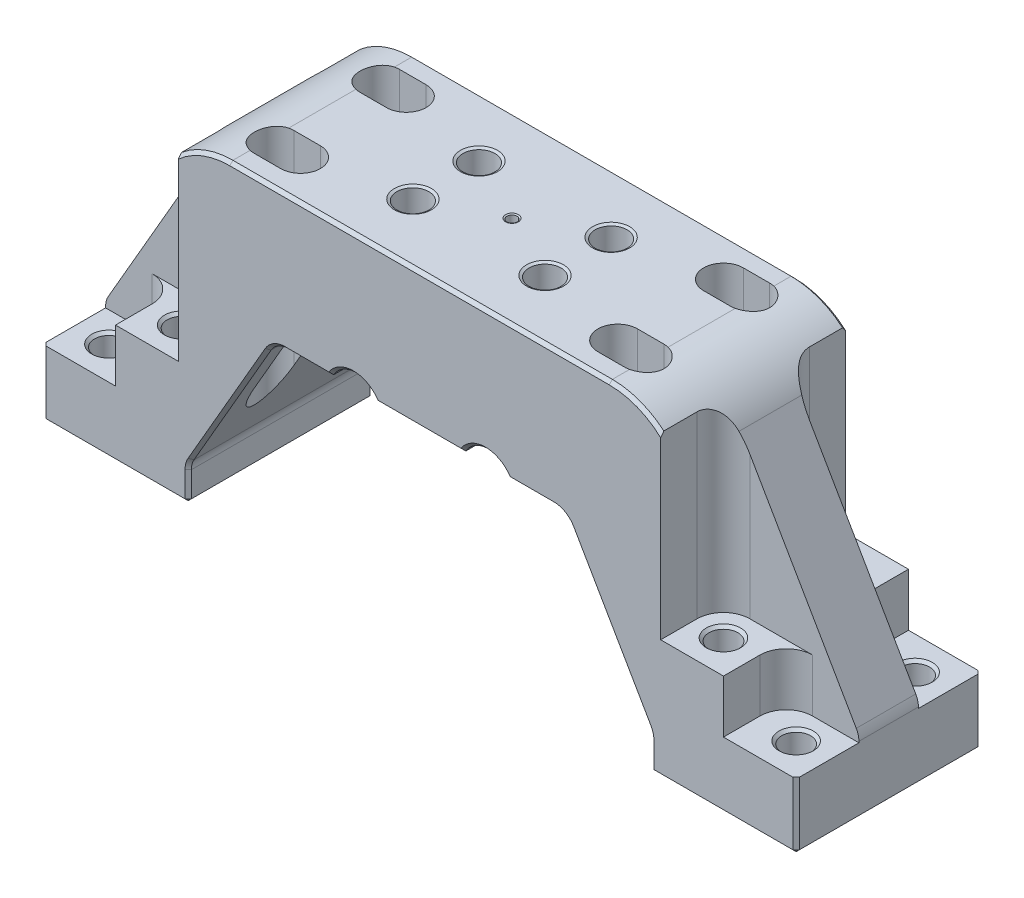
SolidWorks part; units mm, degrees
material "6061-T6 AL"
ref_plane "Front" through (0, 0, 0) normal (0, 0, 1) x (1, 0, 0)
ref_plane "Top" through (0, 0, 0) normal (0, 1, 0) x (1, 0, 0)
ref_plane "Right" through (0, 0, 0) normal (1, 0, 0) x (0, 0, -1)
sketch "Sketch1" plane through (0, 0, 0) normal (0, 0, 1) x (1, 0, 0)
  line L0 (-180.975, 0) -> (-111.125, 0)
  line L1 (-111.125, 0) -> (-111.125, 16.2087)
  line L2 (-111.125, 16.2087) -> (-70.0366, 87.376)
  line L3 (-70.0366, 87.376) -> (70.0366, 87.376)
  line L4 (70.0366, 87.376) -> (111.125, 16.2087)
  line L5 (111.125, 16.2087) -> (111.125, 0)
  line L6 (111.125, 0) -> (180.975, 0)
  line L7 (180.975, 0) -> (180.975, 34.925)
  line L8 (180.975, 34.925) -> (113.1508, 152.4)
  line L9 (113.1508, 152.4) -> (-113.1508, 152.4)
  line L10 (-113.1508, 152.4) -> (-180.975, 34.925)
  line L11 (-180.975, 34.925) -> (-180.975, 0)
  line L12 (-111.125, 0) -> (111.125, 0) construction
  point P9 (0, 87.376)
  point P14 (0, 152.4)
  dimension "D1" = 361.95
  dimension "D2" = 34.925
  dimension "D3" = 69.85
  dimension "D4" = 152.4
  dimension "D5" = 60
  dimension "D6" = 87.376
  dimension "D7" = 69.85
extrude "Extrude1" add sketch "Sketch1" along normal mid plane 88.9
fillet "Fillet1" radius 38.1 2 edges at (113.1508, 152.4, 0) (-113.1508, 152.4, 0)
fillet "Fillet2" radius 9.525 4 edges at (111.125, 16.2087, 0) (70.0366, 87.376, 0) (-70.0366, 87.376, 0) (-111.125, 16.2087, 0)
fillet "Fillet5" radius 9.525 2 edges at (-180.975, 34.925, 0) (180.975, 34.925, 0)
sketch "Sketch2" plane through (0, 87.376, 0) normal (0, -1, 0) x (1, 0, 0)
  line L1 (-47.625, 31.75) -> (47.625, 31.75)
  line L2 (-60.325, 19.05) -> (-60.325, -19.05)
  line L3 (-47.625, -31.75) -> (47.625, -31.75)
  line L4 (60.325, 19.05) -> (60.325, -19.05)
  arc A0 (-60.325, 19.05) -> (-47.625, 31.75) centre (-47.625, 19.05) cw
  arc A1 (60.325, 19.05) -> (47.625, 31.75) centre (47.625, 19.05) ccw
  arc A2 (60.325, -19.05) -> (47.625, -31.75) centre (47.625, -19.05) cw
  arc A3 (-47.625, -31.75) -> (-60.325, -19.05) centre (-47.625, -19.05) cw
  point P12 (0, 31.75)
  point P14 (60.325, 0)
  dimension "D1" = 12.7
  dimension "D2" = 63.5
  dimension "D3" = 120.65
extrude "Extrude2" cut sketch "Sketch2" against normal blind 25.4
fillet "Fillet3" radius 3.175 8 edges at (0, 112.776, 31.75) (56.6053, 112.776, 28.0303) (60.325, 112.776, 0) (56.6053, 112.776, -28.0303) (0, 112.776, -31.75) (-56.6053, 112.776, -28.0303) (-60.325, 112.776, 0) (-56.6053, 112.776, 28.0303)
sketch "Sketch3" plane through (0, 152.4, 0) normal (0, 1, 0) x (1, 0, 0)
  line L0 (91.1537, 44.45) -> (-91.1537, 44.45) construction
  line L1 (115.8875, 44.45) -> (180.975, 44.45)
  line L2 (115.8875, 44.45) -> (115.8875, 26.9875)
  line L3 (128.5875, 14.2875) -> (180.975, 14.2875)
  line L4 (180.975, 44.45) -> (180.975, 14.2875)
  line L6 (0, 44.45) -> (0, 0) construction
  line L7 (0, 0) -> (180.975, 0) construction
  line L8 (180.975, -44.45) -> (180.975, -14.2875)
  line L9 (128.5875, -14.2875) -> (180.975, -14.2875)
  line L10 (115.8875, -44.45) -> (115.8875, -26.9875)
  line L11 (115.8875, -44.45) -> (180.975, -44.45)
  line L12 (-115.8875, -44.45) -> (-180.975, -44.45)
  line L13 (-115.8875, -44.45) -> (-115.8875, -26.9875)
  line L14 (-128.5875, -14.2875) -> (-180.975, -14.2875)
  line L15 (-180.975, -44.45) -> (-180.975, -14.2875)
  line L16 (-180.975, 44.45) -> (-180.975, 14.2875)
  line L17 (-128.5875, 14.2875) -> (-180.975, 14.2875)
  line L18 (-115.8875, 44.45) -> (-115.8875, 26.9875)
  line L19 (-115.8875, 44.45) -> (-180.975, 44.45)
  line L20 (180.975, 44.45) -> (180.975, -44.45) construction
  arc A0 (128.5875, 14.2875) -> (115.8875, 26.9875) centre (128.5875, 26.9875) cw
  arc A1 (128.5875, -14.2875) -> (115.8875, -26.9875) centre (128.5875, -26.9875) ccw
  arc A2 (-128.5875, -14.2875) -> (-115.8875, -26.9875) centre (-128.5875, -26.9875) cw
  arc A3 (-128.5875, 14.2875) -> (-115.8875, 26.9875) centre (-128.5875, 26.9875) ccw
  dimension "D1" = 12.7
  dimension "D2" = 28.575
  dimension "D3" = 65.0875
extrude "Extrude3" cut sketch "Sketch3" against normal offset from surface (95.25 mm away) 57.15 up to face at (146.05, 0, 0)
sketch "Sketch4" plane through (0, 57.15, 0) normal (0, 1, 0) x (1, 0, 0)
  line L0 (168.1434, 14.2875) -> (128.5875, 14.2875) construction
  line L1 (180.975, 44.45) -> (146.05, 44.45)
  line L2 (180.975, 44.45) -> (180.975, 14.2875)
  line L3 (180.975, 14.2875) -> (158.75, 14.2875)
  line L4 (146.05, 44.45) -> (146.05, 26.9875)
  line L5 (0, 44.45) -> (0, 0) construction
  line L6 (91.1537, 44.45) -> (-91.1537, 44.45) construction
  line L7 (0, 0) -> (180.975, 0) construction
  line L9 (146.05, -44.45) -> (146.05, -26.9875)
  line L10 (180.975, -14.2875) -> (158.75, -14.2875)
  line L11 (180.975, -44.45) -> (180.975, -14.2875)
  line L12 (180.975, -44.45) -> (146.05, -44.45)
  line L13 (-180.975, -44.45) -> (-146.05, -44.45)
  line L14 (-180.975, -44.45) -> (-180.975, -14.2875)
  line L15 (-180.975, -14.2875) -> (-158.75, -14.2875)
  line L16 (-146.05, -44.45) -> (-146.05, -26.9875)
  line L17 (-146.05, 44.45) -> (-146.05, 26.9875)
  line L18 (-180.975, 14.2875) -> (-158.75, 14.2875)
  line L19 (-180.975, 44.45) -> (-180.975, 14.2875)
  line L20 (-180.975, 44.45) -> (-146.05, 44.45)
  line L21 (180.975, 44.45) -> (180.975, -44.45) construction
  arc A0 (146.05, 26.9875) -> (158.75, 14.2875) centre (158.75, 26.9875) ccw
  arc A1 (115.8875, 26.9875) -> (128.5875, 14.2875) centre (128.5875, 26.9875) ccw construction
  arc A2 (146.05, -26.9875) -> (158.75, -14.2875) centre (158.75, -26.9875) cw
  arc A3 (-146.05, -26.9875) -> (-158.75, -14.2875) centre (-158.75, -26.9875) ccw
  arc A4 (-146.05, 26.9875) -> (-158.75, 14.2875) centre (-158.75, 26.9875) cw
  point P9 (146.05, 14.2875)
  dimension "D1" = 34.925
extrude "Extrude4" cut sketch "Sketch4" against normal offset from surface (25.4 mm away) 31.75 up to face at (146.05, 0, 0)
hole_wizard "1/2 Clearance Hole1" positions "Sketch6" profile "Sketch5" hole size "1/2" standard "Ansi Inch" end condition through all
sketch "Sketch6" plane through (0, 57.15, 0) normal (0, 1, 0) x (-1, 0, 0)
  line L0 (130.175, 0) -> (-130.175, 0) construction
  line L3 (0, -28.575) -> (0, 28.575) construction
  point P0 (-130.175, -28.575)
  point P1 (130.175, -28.575)
  point P3 (130.175, 28.575)
  point P5 (-130.175, 28.575)
  dimension "D1" = 260.35
  dimension "D2" = 57.15
sketch "Sketch5" plane through (130.175, 57.15, -28.575) normal (1, 0, 0) x (0, 0, 1)
  line L0 (0, 0) -> (0, 57.15)
  line L1 (0, 57.15) -> (8.255, 57.15)
  line L2 (6.9456, 55.8406) -> (6.9456, 1.3094)
  line L3 (6.9456, 1.3094) -> (8.255, 0)
  line L5 (8.255, 0) -> (0, 0)
  line L6 (-6.9456, 1.3094) -> (-8.255, 0) construction
  line L7 (8.255, 57.15) -> (6.9456, 55.8406)
  line L8 (-8.255, 57.15) -> (-6.9456, 55.8406) construction
  line L11 (0, -6.35) -> (0, 107.95) construction
  dimension "Thru Hole Dia." = 13.8913
  dimension "Thru Hole Depth" = 57.15
  dimension "Near C'Sink Dia." = 16.51
  dimension "Near C'Sink Angle" = 90
  dimension "Far C'Sink Dia." = 16.51
  dimension "Far C'Sink Angle" = 90
hole_wizard "1/2 Clearance Hole2" positions "Sketch8" profile "Sketch7" hole size "1/2" standard "Ansi Inch" end condition through all
sketch "Sketch8" plane through (0, 31.75, 0) normal (0, 1, 0) x (-1, 0, 0)
  line L0 (165.1, -28.575) -> (130.175, -28.575) construction
  line L3 (-130.175, -28.575) -> (-165.1, -28.575) construction
  point P0 (-165.1, -28.575)
  point P1 (-165.1, 28.575)
  point P3 (165.1, 28.575)
  point P5 (165.1, -28.575)
  dimension "D1" = 330.2
sketch "Sketch7" plane through (165.1, 31.75, -28.575) normal (1, 0, 0) x (0, 0, 1)
  line L0 (0, 0) -> (0, 31.75)
  line L1 (0, 31.75) -> (8.255, 31.75)
  line L2 (6.9456, 30.4406) -> (6.9456, 1.3094)
  line L3 (6.9456, 1.3094) -> (8.255, 0)
  line L5 (8.255, 0) -> (0, 0)
  line L6 (-6.9456, 1.3094) -> (-8.255, 0) construction
  line L7 (8.255, 31.75) -> (6.9456, 30.4406)
  line L8 (-8.255, 31.75) -> (-6.9456, 30.4406) construction
  line L11 (0, -6.35) -> (0, 107.95) construction
  dimension "Thru Hole Dia." = 13.8913
  dimension "Thru Hole Depth" = 31.75
  dimension "Near C'Sink Dia." = 16.51
  dimension "Near C'Sink Angle" = 90
  dimension "Far C'Sink Dia." = 16.51
  dimension "Far C'Sink Angle" = 90
hole_wizard "Tapped Hole for 1/2-13 Helicoil1" positions "Sketch10" profile "Sketch9" tap size "1/2-13" standard "Helicoil® Inch" end condition up to next
sketch "Sketch10" plane through (0, 152.4, 0) normal (0, 1, 0) x (-1, 0, 0)
  line L0 (31.75, 0) -> (-31.75, 0) construction
  line L3 (0, -15.875) -> (0, 15.875) construction
  point P0 (31.75, -15.875)
  point P1 (-31.75, -15.875)
  point P3 (-31.75, 15.875)
  point P5 (31.75, 15.875)
  dimension "D1" = 31.75
  dimension "D2" = 63.5
sketch "Sketch9" plane through (-31.75, 152.4, -15.875) normal (1, 0, 0) x (0, 0, 1)
  line L0 (0, 0) -> (0, 39.624)
  line L1 (0, 39.624) -> (6.5481, 39.624)
  line L3 (6.5481, 39.624) -> (6.5481, 29.972)
  line L4 (7.6733, 29.972) -> (6.5481, 29.972)
  line L5 (7.6733, 29.972) -> (7.6733, 0.7024)
  line L6 (7.6733, 0.7024) -> (8.89, 0)
  line L7 (8.89, 0) -> (0, 0)
  line L8 (-7.6733, 0.7024) -> (-8.89, 0) construction
  line L11 (0, -6.35) -> (0, 107.95) construction
  dimension "Thru Tap Drill Dia." = 13.0962
  dimension "Thru Tap Drill Depth" = 39.624
  dimension "Thread Major Dia." = 15.3467
  dimension "Thread Depth" = 29.972
  dimension "Near C'Sink Dia." = 17.78
  dimension "Near C'Sink Angle" = 120
sketch "Sketch11" plane through (0, 152.4, 0) normal (0, 1, 0) x (1, 0, 0)
  line L0 (-88.9, 25.4) -> (-76.2, 25.4) construction
  line L1 (-88.9, 34.925) -> (-76.2, 34.925)
  line L2 (-88.9, 15.875) -> (-76.2, 15.875)
  line L3 (-88.9, -25.4) -> (-76.2, -25.4) construction
  line L4 (-88.9, -15.875) -> (-76.2, -15.875)
  line L5 (-88.9, -34.925) -> (-76.2, -34.925)
  line L6 (76.2, 25.4) -> (88.9, 25.4) construction
  line L7 (76.2, 34.925) -> (88.9, 34.925)
  line L8 (76.2, 15.875) -> (88.9, 15.875)
  line L9 (76.2, -25.4) -> (88.9, -25.4) construction
  line L10 (76.2, -15.875) -> (88.9, -15.875)
  line L11 (76.2, -34.925) -> (88.9, -34.925)
  line L12 (-82.55, 0) -> (82.55, 0) construction
  line L13 (0, 25.4) -> (0, -25.4) construction
  arc A0 (-88.9, 34.925) -> (-88.9, 15.875) centre (-88.9, 25.4) ccw
  arc A1 (-76.2, 15.875) -> (-76.2, 34.925) centre (-76.2, 25.4) ccw
  arc A2 (-88.9, -15.875) -> (-88.9, -34.925) centre (-88.9, -25.4) ccw
  arc A3 (-76.2, -34.925) -> (-76.2, -15.875) centre (-76.2, -25.4) ccw
  arc A4 (76.2, 34.925) -> (76.2, 15.875) centre (76.2, 25.4) ccw
  arc A5 (88.9, 15.875) -> (88.9, 34.925) centre (88.9, 25.4) ccw
  arc A6 (76.2, -15.875) -> (76.2, -34.925) centre (76.2, -25.4) ccw
  arc A7 (88.9, -34.925) -> (88.9, -15.875) centre (88.9, -25.4) ccw
  point P2 (-82.55, 25.4)
  point P7 (-82.55, -25.4)
  point P14 (82.55, 25.4)
  point P21 (82.55, -25.4)
  dimension "D1" = 50.8
  dimension "D2" = 165.1
  dimension "D3" = 12.7
  dimension "D4" = 19.05
extrude "Extrude5" cut sketch "Sketch11" against normal through all
sketch "Sketch12" plane through (0, 0, 0) normal (0, 0, 1) x (1, 0, 0)
  line L0 (-31.75, 81.026) -> (31.75, 81.026) construction
  line L1 (0, -48.895) -> (0, 48.895) construction
  line L2 (-64.5373, 87.376) -> (64.5373, 87.376) construction
  circle A0 centre (-31.75, 81.026) radius 12.7
  circle A1 centre (31.75, 81.026) radius 12.7
  point P4 (0, 81.026)
  dimension "D2" = 25.4
  dimension "D1" = 63.5
  dimension "D3" = 6.35
extrude "Extrude6" cut sketch "Sketch12" against normal through all and the other way through all
chamfer "Chamfer1" distance 1.524 angle 45 60 edges at (180.975, 15.875, -44.45) (180.975, 15.875, 44.45) (-180.975, 15.875, -44.45) (-180.975, 15.875, 44.45) (53.6429, 87.376, -44.45) (53.6429, 87.376, 44.45) (69.2998, 86.0999, -44.45) (69.2998, 86.0999, 44.45) (91.3175, 50.5163, -44.45) (91.3175, 50.5163, 44.45) (110.8004, 16.1218, -44.45) (110.8004, 16.1218, 44.45) (111.125, 6.8283, -44.45) (111.125, 6.8283, 44.45) (111.125, 0, 0) (146.05, 0, -44.45) (146.05, 0, 44.45) (180.975, 0, 0) (-53.6429, 87.376, -44.45) (-53.6429, 87.376, 44.45) (-69.2998, 86.0999, -44.45) (-69.2998, 86.0999, 44.45) (-91.3175, 50.5163, -44.45) (-91.3175, 50.5163, 44.45) (-110.8004, 16.1218, -44.45) (-110.8004, 16.1218, 44.45) (-111.125, 6.8283, -44.45) (-111.125, 6.8283, 44.45) (-180.975, 0, 0) (-146.05, 0, -44.45) (-111.125, 0, 0) (-146.05, 0, 44.45) (-45.1868, 87.376, 31.75) (-45.1868, 87.376, -31.75) (-56.6053, 87.376, 28.0303) (-56.6053, 87.376, -28.0303) (-60.325, 87.376, 0) (45.1868, 87.376, -31.75) (45.1868, 87.376, 31.75) (56.6053, 87.376, -28.0303) (56.6053, 87.376, 28.0303) (60.325, 87.376, 0) (-31.75, 93.726, -31.75) (31.75, 93.726, -31.75) (0, 87.376, -31.75) (31.75, 93.726, 31.75) (0, 87.376, 31.75) (-31.75, 93.726, 31.75) (-31.75, 93.726, 44.45) (31.75, 93.726, 44.45) (0, 87.376, 44.45) (31.75, 93.726, -44.45) (0, 87.376, -44.45) (-31.75, 93.726, -44.45) (104.3345, 150.0474, 44.45) (-104.3345, 150.0474, 44.45) (0, 152.4, 44.45) (104.3345, 150.0474, -44.45) (-104.3345, 150.0474, -44.45) (0, 152.4, -44.45)
hole_wizard "#10-32 Tapped Hole1" positions "Sketch20" profile "Sketch19" tap size "#10-32" standard "Ansi Inch"
sketch "Sketch20" plane through (0, 152.4, 0) normal (0, 1, 0) x (-1, 0, 0)
  point P0 (0, 0)
sketch "Sketch19" plane through (0, 152.4, 0) normal (1, 0, 0) x (0, 0, 1)
  line L0 (0, 0) -> (0, 20.2633)
  line L1 (0, 20.2633) -> (2.0193, 19.05)
  line L2 (2.0193, 19.05) -> (2.0193, 11.43)
  line L3 (2.0193, 11.43) -> (2.413, 11.43)
  line L5 (2.413, 11.43) -> (2.413, 0.3666)
  line L6 (2.413, 0.3666) -> (3.048, 0)
  line L7 (3.048, 0) -> (0, 0)
  line L8 (-2.413, 0.3666) -> (-3.048, 0) construction
  line L10 (0, 20.2633) -> (-2.0193, 19.05) construction
  line L11 (0, -6.35) -> (0, 107.95) construction
  dimension "Tap Drill Dia." = 4.0386
  dimension "Tap Drill Depth" = 19.05
  dimension "Thread Major Dia." = 4.826
  dimension "Thread Depth" = 11.43
  dimension "Near C'Sink Dia." = 6.096
  dimension "Near C'Sink Angle" = 120
  dimension "Drill Angle" = 118
